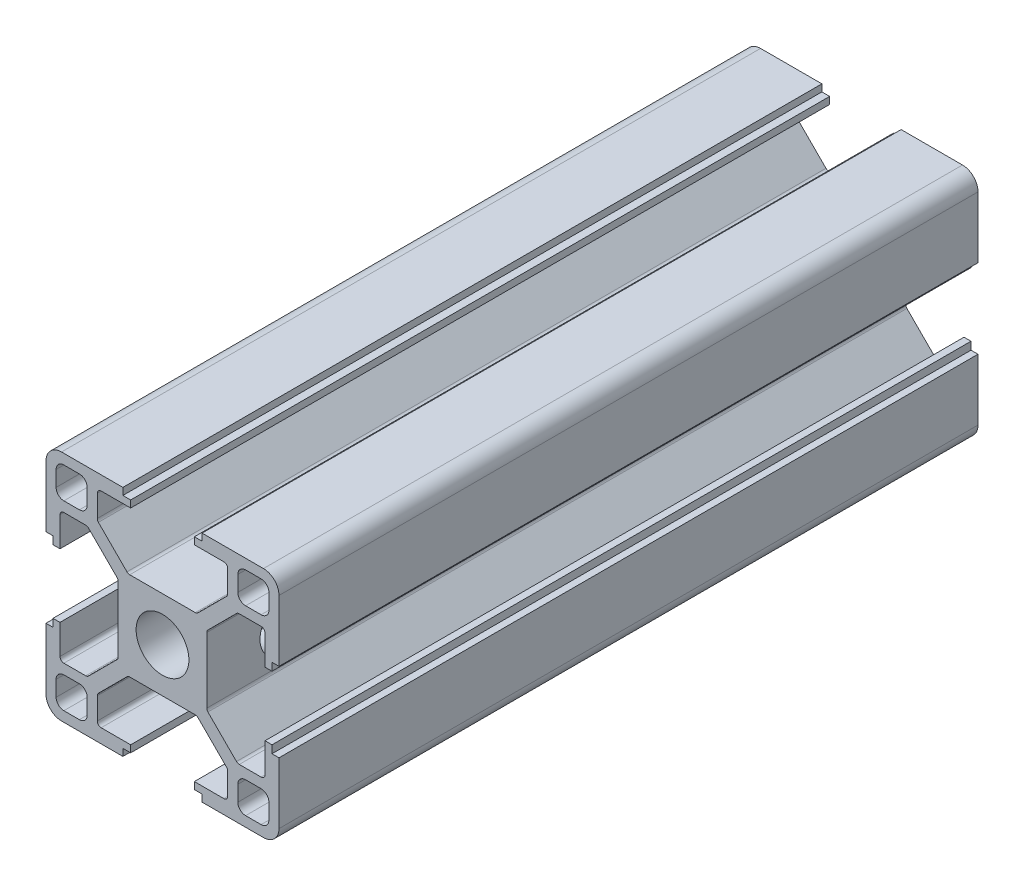
SolidWorks part; units mm, degrees
ref_plane "前视基准面" through (0, 0, 0) normal (0, 0, 1) x (1, 0, 0)
ref_plane "上视基准面" through (0, 0, 0) normal (0, 1, 0) x (1, 0, 0)
ref_plane "右视基准面" through (0, 0, 0) normal (1, 0, 0) x (0, 0, -1)
sketch "草图1" plane through (0, 0, 0) normal (0, 0, 1) x (1, 0, 0)
  line L0 (0, 0) -> (0, 65.3905) construction
  line L1 (0, 0) -> (64.2648, 0) construction
  line L2 (0, 0) -> (79.9729, 79.9729) construction
  line L3 (5.7, 0) -> (5.7, 4.4272)
  line L4 (5.7, 4.4272) -> (9.6728, 8.4)
  line L5 (9.6728, 8.4) -> (13.2, 8.4)
  line L6 (13.2, 8.4) -> (13.2, 4.1)
  line L7 (13.2, 4.1) -> (14.1, 4.1)
  line L8 (14.1, 4.1) -> (14.1, 5.1)
  line L9 (14.1, 5.1) -> (15, 5.1)
  line L10 (15, 5.1) -> (15, 15)
  line L11 (5.1, 15) -> (15, 15)
  line L12 (5.1, 14.1) -> (5.1, 15)
  line L13 (4.1, 14.1) -> (5.1, 14.1)
  line L14 (4.1, 13.2) -> (4.1, 14.1)
  line L15 (8.4, 13.2) -> (4.1, 13.2)
  line L16 (8.4, 9.6728) -> (8.4, 13.2)
  line L17 (4.4272, 5.7) -> (8.4, 9.6728)
  line L18 (0, 5.7) -> (4.4272, 5.7)
  line L20 (9.7, 9.7) -> (13.7, 9.7)
  line L21 (9.7, 9.7) -> (9.7, 13.7)
  line L22 (9.7, 13.7) -> (13.7, 13.7)
  line L23 (13.7, 9.7) -> (13.7, 13.7)
  line L24 (9.7, 9.7) -> (13.7, 13.7) construction
  line L25 (9.7, 13.7) -> (13.7, 9.7) construction
  line L26 (0, 5.7) -> (0, 0)
  line L27 (0, 0) -> (5.7, 0)
  point P9 (11.7, 11.7)
  dimension "D1" = 45
  dimension "D2" = 5.7
  dimension "D3" = 1.8
  dimension "D4" = 0.9
  dimension "D5" = 8.2
  dimension "D6" = 10.2
  dimension "D7" = 1.8
  dimension "D8" = 15
  dimension "D9" = 16.8
  dimension "D10" = 4
  dimension "D11" = 1.3
extrude "凸台-拉伸1" add sketch "草图1" along normal blind 90 contours L3 L4 L5 L6 L7 L8 L9 L10 L11 L12 L13 L14 L15 L16 L17 L18 L26 L27
fillet "圆角1" radius 1 4 edges at (9.7, 9.7, 45) (13.7, 9.7, 45) (9.7, 13.7, 45) (13.7, 13.7, 45)
fillet "圆角2" radius 2 1 edges at (15, 15, 45)
fillet "圆角3" radius 0.5 6 edges at (5.7, 4.4272, 45) (4.4272, 5.7, 45) (8.4, 13.2, 45) (8.4, 9.6728, 45) (9.6728, 8.4, 45) (13.2, 8.4, 45)
pattern_circular "阵列(圆周)1" count 4 over 360 about axis through (0, 0, 0) along (0, 0, 1) of "圆角2", "圆角3", "凸台-拉伸1", "圆角1"
sketch "草图2" plane through (0, 0, 90) normal (0, 0, 1) x (1, 0, 0)
  circle A0 centre (0, 0) radius 3.4
  dimension "D1" = 6.8
extrude "切除-拉伸1" cut sketch "草图2" against normal through all
sketch "草图3" plane through (-5.7, 0, 0) normal (-1, 0, 0) x (0, 0, 1)
  line L0 (-5.668, 0) -> (141.0871, 0) construction
  line L1 (0, -4.2201) -> (0, 4.2201) construction
  line L2 (90, 4.2201) -> (90, -4.2201) construction
  circle A0 centre (15, 0) radius 3.15
  circle A1 centre (80, 0) radius 3.15
  circle A2 centre (31, 0) radius 3.15
  point P11 (107.6335, 0)
  dimension "D1" = 6.3
  dimension "D2" = 15
  dimension "D3" = 49
  dimension "D4" = 10
extrude "切除-拉伸2" cut sketch "草图3" against normal through all
